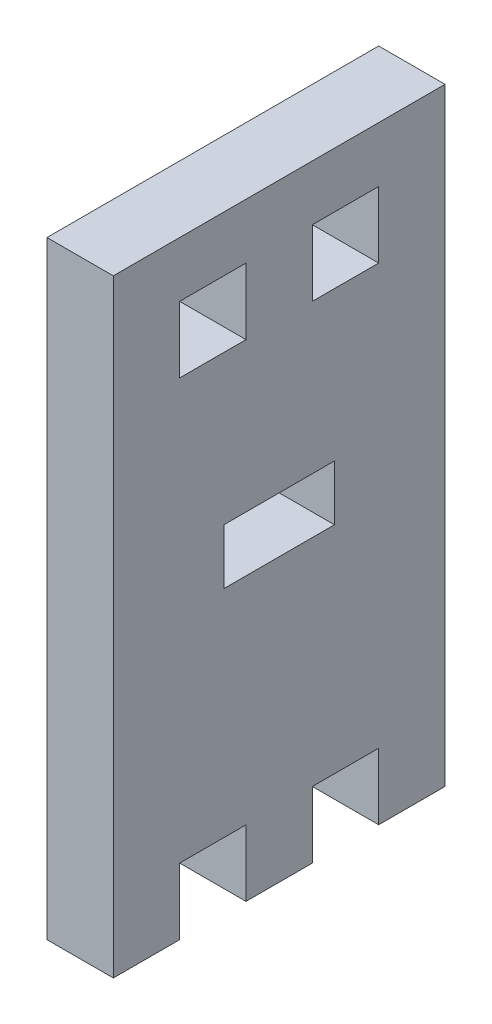
SolidWorks part; units mm, degrees
ref_plane "Front" through (0, 0, 0) normal (0, 0, 1) x (1, 0, 0)
ref_plane "Top" through (0, 0, 0) normal (0, 1, 0) x (1, 0, 0)
ref_plane "Right" through (0, 0, 0) normal (1, 0, 0) x (0, 0, -1)
sketch "Sketch1" plane through (0, 0, 0) normal (1, 0, 0) x (0, 0, -1)
  line L0 (-18.5982, 0) -> (21.6004, 0) construction
  line L1 (-15, 27.5) -> (15, 27.5)
  line L2 (-15, 27.5) -> (-15, -27.5)
  line L3 (-15, -27.5) -> (-9, -27.5)
  line L4 (15, 27.5) -> (15, -27.5)
  line L5 (-15, 27.5) -> (15, -27.5) construction
  line L6 (-15, -27.5) -> (15, 27.5) construction
  line L7 (-9, 22.5) -> (-3, 22.5)
  line L8 (-9, 22.5) -> (-9, 16.5)
  line L9 (-9, 16.5) -> (-3, 16.5)
  line L10 (-3, 22.5) -> (-3, 16.5)
  line L11 (-9, 22.5) -> (-3, 16.5) construction
  line L12 (-9, 16.5) -> (-3, 22.5) construction
  line L17 (0, 29.142) -> (0, -28.9726) construction
  line L22 (9, 22.5) -> (9, 16.5)
  line L23 (9, 22.5) -> (3, 22.5)
  line L24 (3, 22.5) -> (3, 16.5)
  line L25 (9, 16.5) -> (3, 16.5)
  line L27 (-3, -21.5) -> (-9, -21.5)
  line L28 (-3, -21.5) -> (-3, -27.5)
  line L30 (-9, -21.5) -> (-9, -27.5)
  line L31 (-3, -21.5) -> (-9, -27.5) construction
  line L32 (-3, -27.5) -> (-9, -21.5) construction
  line L34 (9, -21.5) -> (9, -27.5)
  line L35 (3, -21.5) -> (9, -21.5)
  line L36 (3, -21.5) -> (3, -27.5)
  line L37 (9, -27.5) -> (15, -27.5)
  line L38 (-3, -27.5) -> (3, -27.5)
  line L40 (5, -2) -> (-5, -2)
  line L41 (5, -2) -> (5, 3)
  line L42 (5, 3) -> (-5, 3)
  line L43 (-5, -2) -> (-5, 3)
  line L44 (5, -2) -> (-5, 3) construction
  line L45 (5, 3) -> (-5, -2) construction
  point P0 (0, 0)
  point P6 (-6, 19.5)
  point P15 (-6, 22.5)
  point P16 (-6, -24.5)
  point P29 (0, 0.5)
  dimension "D1" = 30
  dimension "D2" = 55
  dimension "D4" = 6
  dimension "D5" = 6
  dimension "D3" = 3
  dimension "D6" = 5
  dimension "D7" = 16
  dimension "D8" = 5
  dimension "D9" = 10
extrude "Boss-Extrude1" add sketch "Sketch1" along normal blind 6 contours L28 L38 L36 L35 L34 L37 L4 L1 L2 L3 L30 L27 L22 L25 L24 L23 L7 L10 L9 L8
equation "\"D2@Sketch1\"=50+\"D6@Sketch1\""
